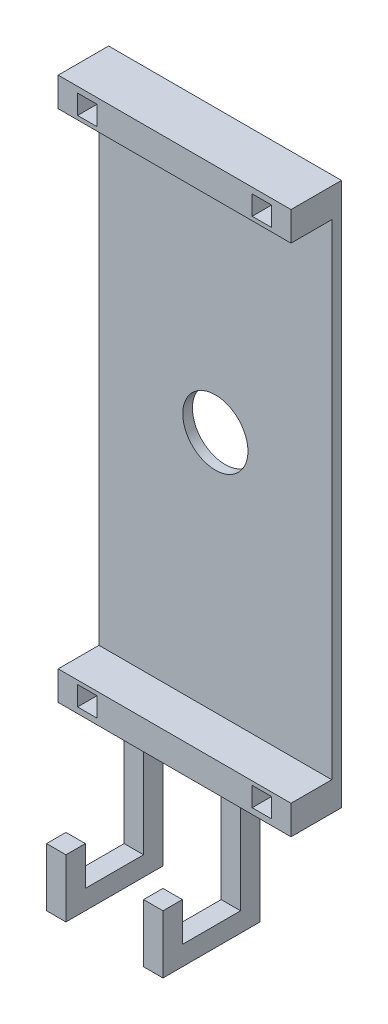
SolidWorks part; units mm, degrees
ref_plane "Front Plane" through (0, 0, 0) normal (0, 0, 1) x (1, 0, 0)
ref_plane "Top Plane" through (0, 0, 0) normal (0, 1, 0) x (1, 0, 0)
ref_plane "Right Plane" through (0, 0, 0) normal (1, 0, 0) x (0, 0, -1)
sketch "Sketch2" plane through (0, 0, 0) normal (0, 0, 1) x (1, 0, 0)
  line L0 (0, 0) -> (70, 0)
  line L1 (70, 0) -> (70, 140)
  line L2 (70, 140) -> (0, 140)
  line L3 (0, 140) -> (0, 0)
  dimension "D1" = 140
  dimension "D2" = 70
extrude "Boss-Extrude1" add sketch "Sketch2" along normal blind 15
sketch "Sketch7" plane through (0, 0, 15) normal (0, 0, 1) x (1, 0, 0)
  line L0 (35, 140) -> (35, 0) construction
  line L1 (70, 140) -> (0, 140) construction
  line L2 (0, 0) -> (70, 0) construction
  line L3 (0, 70) -> (70, 70) construction
  line L4 (0, 140) -> (0, 0) construction
  line L5 (70, 0) -> (70, 140) construction
  line L7 (70, 7.5) -> (0, 7.5)
  line L8 (70, 7.5) -> (70, 132.5)
  line L9 (70, 132.5) -> (0, 132.5)
  line L10 (0, 7.5) -> (0, 132.5)
  line L11 (70, 7.5) -> (0, 132.5) construction
  line L12 (70, 132.5) -> (0, 7.5) construction
  point P12 (35, 70)
  dimension "D1" = 7.5
  dimension "D2" = 7.5
extrude "Cut-Extrude4" cut sketch "Sketch7" against normal blind 12.5
sketch "Sketch8" plane through (0, 0, 15) normal (0, 0, 1) x (1, 0, 0)
  line L0 (35, 140) -> (35, 0) construction
  line L1 (70, 140) -> (0, 140) construction
  line L2 (0, 0) -> (70, 0) construction
  line L3 (0, 70) -> (70, 70) construction
  line L4 (0, 132.5) -> (0, 7.5) construction
  line L5 (70, 7.5) -> (70, 132.5) construction
  line L23 (0, 140) -> (0, 132.5) construction
  line L24 (15, 133.5) -> (10, 133.5)
  line L25 (15, 133.5) -> (15, 138.5)
  line L26 (15, 138.5) -> (10, 138.5)
  line L27 (10, 133.5) -> (10, 138.5)
  line L28 (15, 133.5) -> (10, 138.5) construction
  line L29 (15, 138.5) -> (10, 133.5) construction
  line L31 (55, 133.5) -> (60, 133.5)
  line L32 (55, 133.5) -> (55, 138.5)
  line L33 (60, 133.5) -> (60, 138.5)
  line L34 (55, 138.5) -> (60, 138.5)
  line L35 (10, 6.5) -> (10, 1.5)
  line L36 (15, 6.5) -> (10, 6.5)
  line L37 (15, 6.5) -> (15, 1.5)
  line L38 (15, 1.5) -> (10, 1.5)
  line L39 (60, 6.5) -> (60, 1.5)
  line L40 (55, 1.5) -> (60, 1.5)
  line L41 (55, 6.5) -> (55, 1.5)
  line L42 (55, 6.5) -> (60, 6.5)
  point P12 (12.5, 136)
  dimension "D1" = 10
  dimension "D2" = 1.5
  dimension "D3" = 5
  dimension "D4" = 5
extrude "Cut-Extrude5" cut sketch "Sketch8" against normal blind 7
sketch "Sketch6" plane through (0, 0, 0) normal (0, 0, -1) x (-1, 0, 0)
  line L0 (-35, 140) -> (-35, 0) construction
  line L1 (-70, 140) -> (0, 140) construction
  line L2 (0, 0) -> (-70, 0) construction
  line L3 (0, 70) -> (-70, 70) construction
  line L4 (0, 140) -> (0, 0) construction
  line L5 (-70, 0) -> (-70, 140) construction
  circle A0 centre (-35, 70) radius 8.4
  dimension "D1" = 16.8
extrude "Cut-Extrude2" cut sketch "Sketch6" against normal through all
sketch "Sketch9" plane through (0, 0, 0) normal (0, 0, -1) x (-1, 0, 0)
  line L0 (-70, 140) -> (0, 140) construction
  line L1 (-65, 140) -> (-5, 140)
  line L2 (-65, 140) -> (-65, 0)
  line L3 (-65, 0) -> (-5, 0)
  line L4 (-5, 140) -> (-5, 0)
  line L5 (0, 0) -> (-70, 0) construction
  line L6 (-70, 0) -> (-70, 140) construction
  line L7 (0, 140) -> (0, 0) construction
  dimension "D1" = 5
  dimension "D2" = 5
extrude "Cut-Extrude6" cut sketch "Sketch9" against normal blind 15 flip side to cut
sketch "Sketch10" plane through (0, 140, 0) normal (0, 1, 0) x (1, 0, 0)
  line L0 (65, -15) -> (65, 0) construction
  line L1 (5, -15) -> (65, -15)
  line L2 (5, -15) -> (5, -13)
  line L3 (5, -13) -> (65, -13)
  line L4 (65, -15) -> (65, -13)
  dimension "D1" = 2
extrude "Cut-Extrude7" cut sketch "Sketch10" against normal blind 140
sketch "Sketch11" plane through (0, 0, 0) normal (0, -1, 0) x (1, 0, 0)
  line L0 (5, 6.5) -> (65, 6.5) construction
  line L1 (5, 13) -> (5, 0) construction
  line L2 (65, 13) -> (65, 0) construction
  line L3 (35, 13) -> (35, 0) construction
  line L4 (65, 13) -> (5, 13) construction
  line L5 (5, 0) -> (65, 0) construction
  line L6 (45, 6) -> (50, 6)
  line L7 (25, 6) -> (20, 6)
  line L8 (25, 6) -> (25, 11)
  line L9 (25, 11) -> (20, 11)
  line L10 (20, 6) -> (20, 11)
  line L11 (25, 6) -> (20, 11) construction
  line L12 (25, 11) -> (20, 6) construction
  line L13 (50, 6) -> (50, 11)
  line L14 (45, 11) -> (50, 11)
  line L15 (45, 6) -> (45, 11)
  point P12 (22.5, 8.5)
  dimension "D1" = 5
  dimension "0.5" = 5
  dimension "D2" = 2
  dimension "D3" = 10
extrude "Boss-Extrude2" add sketch "Sketch11" along normal blind 30
sketch "Sketch12" plane through (0, 0, 11) normal (0, 0, 1) x (1, 0, 0)
  line L0 (25, -30) -> (25, 0) construction
  line L1 (20, -30) -> (25, -30)
  line L2 (20, -30) -> (20, -25)
  line L3 (20, -25) -> (25, -25)
  line L4 (25, -30) -> (25, -25)
  dimension "D1" = 5
  dimension "D2" = 5
extrude "Boss-Extrude3" add sketch "Sketch12" along normal blind 20
sketch "Sketch13" plane through (0, -25, 0) normal (0, 1, 0) x (1, 0, 0)
  line L0 (25, -31) -> (25, -11) construction
  line L1 (20, -31) -> (25, -31)
  line L2 (20, -31) -> (20, -26)
  line L3 (20, -26) -> (25, -26)
  line L4 (25, -31) -> (25, -26)
  dimension "D1" = 5
  dimension "D2" = 5
extrude "Boss-Extrude4" add sketch "Sketch13" along normal blind 10
sketch "Sketch15" plane through (0, 0, 11) normal (0, 0, 1) x (1, 0, 0)
  line L0 (50, -30) -> (50, 0) construction
  line L1 (45, -30) -> (50, -30)
  line L2 (45, -30) -> (45, -25)
  line L3 (45, -25) -> (50, -25)
  line L4 (50, -30) -> (50, -25)
  dimension "D1" = 5
extrude "Boss-Extrude5" add sketch "Sketch15" along normal blind 20
sketch "Sketch16" plane through (0, -25, 0) normal (0, 1, 0) x (1, 0, 0)
  line L0 (50, -31) -> (50, -11) construction
  line L1 (45, -31) -> (50, -31)
  line L2 (45, -31) -> (45, -26)
  line L3 (45, -26) -> (50, -26)
  line L4 (50, -31) -> (50, -26)
  dimension "D1" = 5
extrude "Boss-Extrude6" add sketch "Sketch16" along normal blind 10
